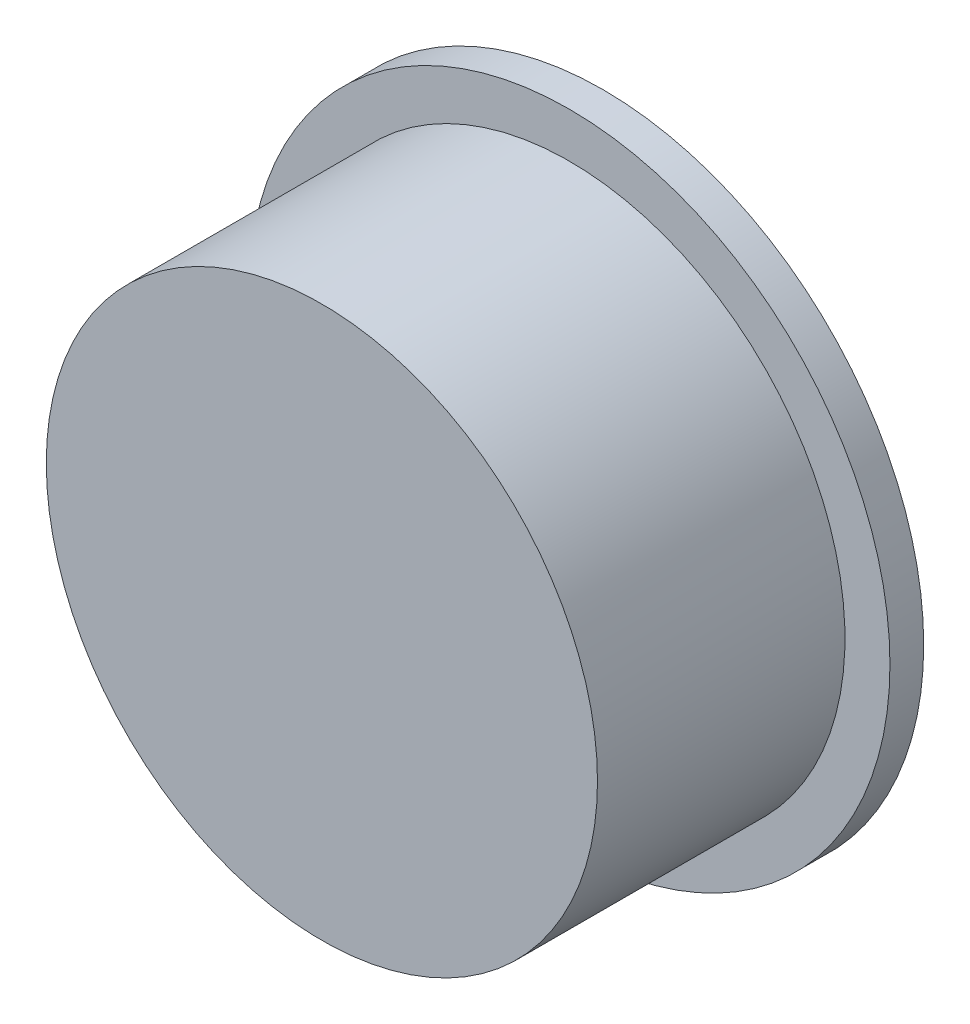
SolidWorks part; units mm, degrees
ref_plane "Front Plane" through (0, 0, 0) normal (0, 0, 1) x (1, 0, 0)
ref_plane "Top Plane" through (0, 0, 0) normal (0, 1, 0) x (1, 0, 0)
ref_plane "Right Plane" through (0, 0, 0) normal (1, 0, 0) x (0, 0, -1)
sketch "Sketch1" plane through (0, 0, 0) normal (0, 0, 1) x (1, 0, 0)
  circle A0 centre (-8.5227, 9.1777) radius 24.5
  circle A1 centre (-8.5227, 9.1777) radius 22.5
  dimension "D1" = 49
  dimension "D2" = 2
extrude "Boss-Extrude1" add sketch "Sketch1" against normal blind 15 and the other way blind 10
sketch "Sketch2" plane through (0, 0, 10) normal (0, 0, 1) x (1, 0, 0)
  circle A0 centre (-8.5227, 9.1777) radius 22.7359
extrude "Boss-Extrude2" add sketch "Sketch2" against normal blind 2
sketch "Sketch3" plane through (0, 0, -15) normal (0, 0, -1) x (-1, 0, 0)
  line L0 (31.0227, 9.1777) -> (-13.9773, 9.1777) construction
  line L1 (8.5227, 19.1777) -> (8.5227, -0.8223) construction
  line L2 (16.5227, 14.1777) -> (31.0227, 14.1777)
  line L3 (16.5227, 14.1777) -> (16.5227, 4.1777)
  line L4 (16.5227, 4.1777) -> (31.0227, 4.1777)
  line L5 (31.0227, 14.1777) -> (31.0227, 4.1777)
  line L6 (0.5227, 4.1777) -> (-13.9773, 4.1777)
  line L7 (-13.9773, 14.1777) -> (-13.9773, 4.1777)
  line L8 (0.5227, 14.1777) -> (-13.9773, 14.1777)
  line L9 (0.5227, 14.1777) -> (0.5227, 4.1777)
  circle A0 centre (8.5227, 9.1777) radius 22.5 construction
  circle A1 centre (8.5227, 9.1777) radius 10
  point P13 (31.0227, 9.1777)
  circle M6 centre (8.5227, 9.1777) radius 22.5
  dimension "D1" = 20
  dimension "D2" = 5
  dimension "D3" = 5
  dimension "D4" = 8
extrude "Boss-Extrude3" add sketch "Sketch3" against normal blind 2 contours A1 L4 L2 M6 | L4 A1 L2 L3 | L2 A1 L8 L9 L6 L4 L3 | L8 A1 L6 L9 | A1 L8 L6 M6
sketch "Sketch4" plane through (0, 0, -15) normal (0, 0, -1) x (-1, 0, 0)
  circle A0 centre (8.5227, 9.1777) radius 24.5 construction
  circle A1 centre (8.5227, 9.1777) radius 24.5
  circle A3 centre (8.5227, 9.1777) radius 28.5
  point P5 (8.5227, 9.5461)
  point P6 (8.5227, 9.5461)
  point P7 (8.5227, 9.5461)
  point P8 (8.5227, 9.5461)
  point P9 (18.4664, 15.3579)
  dimension "D1" = 4
  dimension "D2" = 0
  dimension "D3" = 0
extrude "Boss-Extrude4" add sketch "Sketch4" against normal blind 3 from offset 0
